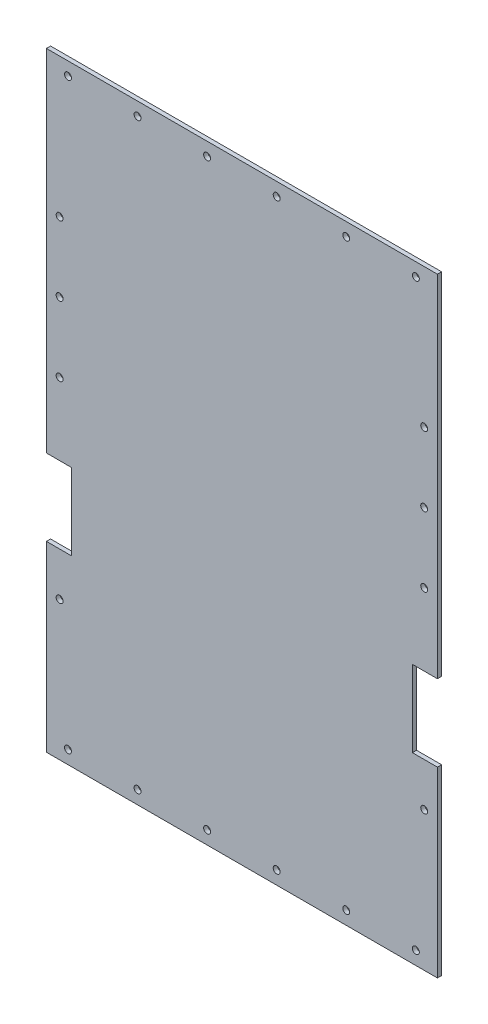
SolidWorks part; units mm, degrees
ref_plane "Front Plane" through (0, 0, 0) normal (0, 0, 1) x (1, 0, 0)
ref_plane "Top Plane" through (0, 0, 0) normal (0, 1, 0) x (1, 0, 0)
ref_plane "Right Plane" through (0, 0, 0) normal (1, 0, 0) x (0, 0, -1)
sketch "Sketch1" plane through (0, 0, 0) normal (0, 0, 1) x (1, 0, 0)
  line L0 (0, 186.26) -> (0, 438.1)
  line L1 (0, 0) -> (281.05, 0)
  line L2 (0, 0) -> (0, 131.26)
  line L3 (0, 438.1) -> (281.05, 438.1)
  line L4 (281.05, 0) -> (281.05, 131.26)
  line L5 (0, 186.26) -> (18, 186.26)
  line L7 (0, 131.26) -> (18, 131.26)
  line L8 (18, 186.26) -> (18, 131.26)
  line L9 (281.05, 186.26) -> (263.05, 186.26)
  line L11 (281.05, 131.26) -> (263.05, 131.26)
  line L12 (263.05, 186.26) -> (263.05, 131.26)
  line L13 (281.05, 186.26) -> (281.05, 438.1)
  dimension "D1" = 438.1
  dimension "D2" = 281.05
  dimension "D3" = 18
  dimension "D4" = 131.26
  dimension "D5" = 55
extrude "Boss-Extrude1" add sketch "Sketch1" along normal blind 3
sketch "Sketch3" plane through (0, 0, 3) normal (0, 0, 1) x (1, 0, 0)
  line L0 (281.05, 438.1) -> (0, 438.1) construction
  line L1 (140.525, 438.1) -> (140.525, 409.6457) construction
  line L2 (0, 219.05) -> (281.05, 219.05) construction
  line L3 (281.05, 186.26) -> (281.05, 438.1) construction
  line L4 (0, 438.1) -> (0, 186.26) construction
  line L7 (0, 0) -> (281.05, 0) construction
  circle A0 centre (65.525, 428.6) radius 2.5
  circle A1 centre (115.525, 428.6) radius 2.5
  circle A2 centre (15.525, 428.6) radius 2.5
  circle A3 centre (265.525, 428.6) radius 2.5
  circle A4 centre (165.525, 428.6) radius 2.5
  circle A5 centre (215.525, 428.6) radius 2.5
  circle A6 centre (215.525, 9.5) radius 2.5
  circle A7 centre (165.525, 9.5) radius 2.5
  circle A8 centre (265.525, 9.5) radius 2.5
  circle A9 centre (15.525, 9.5) radius 2.5
  circle A10 centre (115.525, 9.5) radius 2.5
  circle A11 centre (65.525, 9.5) radius 2.5
  circle A12 centre (9.5, 338.1) radius 2.5
  circle A13 centre (9.5, 288.1) radius 2.5
  circle A14 centre (9.5, 238.1) radius 2.5
  circle A15 centre (9.5, 100) radius 2.5
  circle A16 centre (271.55, 100) radius 2.5
  circle A17 centre (271.55, 238.1) radius 2.5
  circle A18 centre (271.55, 288.1) radius 2.5
  circle A19 centre (271.55, 338.1) radius 2.5
  point P44 (0, 0)
  dimension "D2" = 5
  dimension "D3" = 25
  dimension "D4" = 50
  dimension "D5" = 50
  dimension "D7" = 9.5
  dimension "D9" = 50
  dimension "D10" = 50
  dimension "D11" = 100
  dimension "D1" = 9.5
  dimension "D6" = 219.05
  dimension "D8" = 100
extrude "Cut-Extrude1" cut sketch "Sketch3" against normal through all
